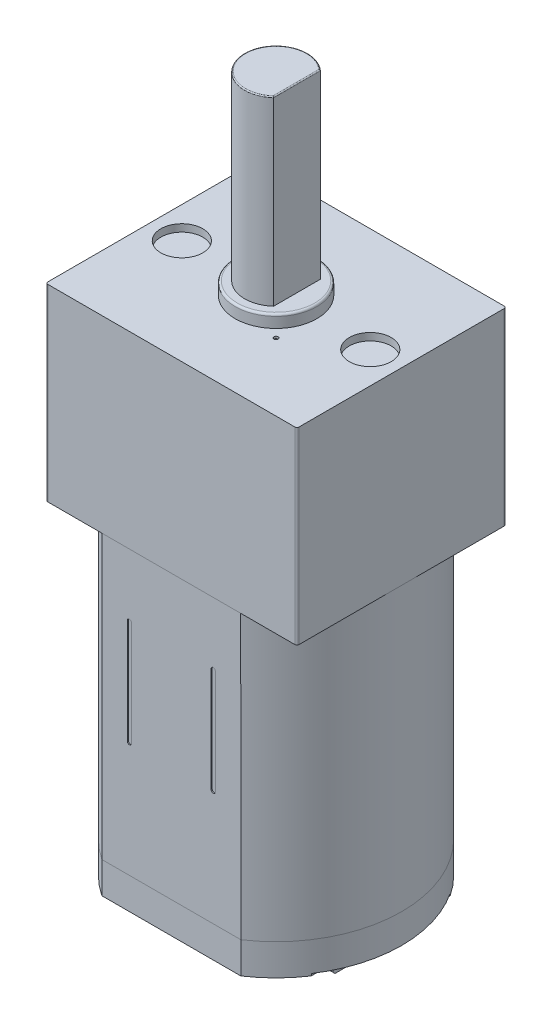
SolidWorks part; units mm, degrees
ref_plane "Спереди" through (0, 0, 0) normal (0, 0, 1) x (1, 0, 0)
ref_plane "Сверху" through (0, 0, 0) normal (0, 1, 0) x (1, 0, 0)
ref_plane "Справа" through (0, 0, 0) normal (1, 0, 0) x (0, 0, -1)
sketch "Эскиз1" plane through (0, 0, 0) normal (0, 1, 0) x (1, 0, 0)
  line L0 (-3.3166, 5) -> (3.3166, 5)
  line L1 (-3.3166, -5) -> (3.3166, -5)
  arc A0 (-3.3166, 5) -> (-3.3166, -5) centre (0, 0) ccw
  arc A1 (3.3166, -5) -> (3.3166, 5) centre (0, 0) ccw
  dimension "D1" = 12
  dimension "D2" = 5
  dimension "D3" = 5
extrude "Бобышка-Вытянуть1" add sketch "Эскиз1" along normal blind 13.5
sketch "Эскиз2" plane through (0, 13.5, 0) normal (0, 1, 0) x (1, 0, 0)
  line L1 (-6, 4.9983) -> (6, 4.9983)
  line L2 (-6, 4.9983) -> (-6, -5.0017)
  line L3 (-6, -5.0017) -> (6, -5.0017)
  line L4 (6, 4.9983) -> (6, -5.0017)
  dimension "D1" = 10
  dimension "D2" = 12
  dimension "D3" = 6
  dimension "D4" = 4.9983
extrude "Бобышка-Вытянуть2" add sketch "Эскиз2" along normal blind 9
sketch "Эскиз3" plane through (0, 22.5, 0) normal (0, 1, 0) x (1, 0, 0)
  circle A0 centre (0, 0) radius 1.95
  dimension "D1" = 3.9
extrude "Бобышка-Вытянуть3" add sketch "Эскиз3" along normal blind 0.6
sketch "Эскиз4" plane through (0, 23.1, 0) normal (0, 1, 0) x (1, 0, 0)
  line L0 (1, 1.118) -> (1, -1.118)
  arc A0 (1, 1.118) -> (1, -1.118) centre (0, 0) ccw
  point P5 (-1.5, 0)
  dimension "D1" = 3
  dimension "D2" = 2.5
extrude "Бобышка-Вытянуть4" add sketch "Эскиз4" along normal blind 8.67
sketch "Эскиз5" plane through (0, 22.5, 0) normal (0, 1, 0) x (1, 0, 0)
  line L0 (0, 4.9983) -> (0, -5.0017) construction
  line L1 (6, 4.9983) -> (-6, 4.9983) construction
  line L2 (-6, -5.0017) -> (6, -5.0017) construction
  circle A0 centre (-4.5, 0) radius 1
  circle A1 centre (4.5, 0) radius 1
  dimension "D3" = 2
  dimension "D1" = 4.5
  dimension "D2" = 4.9983
extrude "Вырез-Вытянуть1" cut sketch "Эскиз5" against normal blind 0.35
fillet "Скругление1" radius 0.1 4 edges
sketch "Эскиз6" plane through (0, 0, 0) normal (0, -1, 0) x (1, 0, 0)
  line L2 (-3.3166, -5) -> (3.3166, -5)
  line L3 (3.3166, 5) -> (-3.3166, 5)
  line L4 (-3.3166, -5) -> (3.3166, -5)
  line L5 (3.3166, 5) -> (-3.3166, 5)
  arc A2 (-3.3166, 5) -> (-3.3166, -5) centre (0, 0) ccw
  arc A3 (3.3166, -5) -> (3.3166, 5) centre (0, 0) ccw
  arc A4 (-3.3166, 5) -> (-3.3166, -5) centre (0, 0) ccw
  arc A5 (3.3166, -5) -> (3.3166, 5) centre (0, 0) ccw
  dimension "D1" = 0
extrude "Бобышка-Вытянуть6" add sketch "Эскиз6" along normal blind 1.4 separate body
sketch "Эскиз7" plane through (0, -1.4, 0) normal (0, -1, 0) x (-1, 0, 0)
  line L0 (5, -3.3166) -> (5, 3.3166)
  line L1 (-5, -3.3166) -> (-5, 3.3166)
  line L2 (3.3166, -5) -> (-3.3166, -5)
  line L3 (3.3166, 5) -> (-3.3176, 4.9987)
  arc A0 (3.3166, -5) -> (3.3166, 5) centre (0, 0) ccw construction
  arc A1 (-3.3166, 5) -> (-3.3166, -5) centre (0, 0) ccw construction
  arc A2 (3.3166, -5) -> (-3.3166, -5) centre (0, 0) ccw
  dimension "D1" = 5
  dimension "D2" = 5
extrude "Бобышка-Вытянуть7" add sketch "Эскиз7" along normal blind 0.1
sketch "Эскиз8" plane through (0, -1.5, 0) normal (0, -1, 0) x (-1, 0, 0)
  line L0 (5, 0) -> (-5, 0) construction
  line L1 (3.465, -0.75) -> (3.165, -0.75)
  line L2 (3.465, -0.75) -> (3.465, 0.75)
  line L3 (3.465, 0.75) -> (3.165, 0.75)
  line L4 (3.165, -0.75) -> (3.165, 0.75)
  line L5 (5, -3.3166) -> (5, 3.3166) construction
  line L6 (-5, -3.3166) -> (-5, 3.3166) construction
  line L7 (0, -5) -> (0, 5) construction
  line L8 (-3.3166, -5) -> (3.3166, -5) construction
  line L9 (3.3166, 5) -> (-3.3166, 5) construction
  line L10 (3.315, -0.75) -> (3.315, 0.75) construction
  line L11 (-3.315, -0.75) -> (-3.315, 0.75) construction
  line L12 (-3.165, -0.75) -> (-3.165, 0.75)
  line L13 (-3.465, 0.75) -> (-3.165, 0.75)
  line L14 (-3.465, -0.75) -> (-3.465, 0.75)
  line L15 (-3.465, -0.75) -> (-3.165, -0.75)
  dimension "D1" = 0.3
  dimension "D2" = 3.315
  dimension "D3" = 1.5
  dimension "D4" = 0.75
extrude "Бобышка-Вытянуть8" add sketch "Эскиз8" along normal blind 2
chamfer "Фаска1" distance 0.1 angle 45 4 edges at (3.315, -3.5, 0.75) (3.315, -3.5, -0.75) (-3.315, -3.5, 0.75) (-3.315, -3.5, -0.75)
sketch "Эскиз9" plane through (-3.465, 0, 0) normal (-1, 0, 0) x (0, 0, 1)
  line L0 (-0.75, -3.4) -> (-0.75, -1.5) construction
  line L1 (0.75, -1.5) -> (-0.75, -1.5) construction
  circle A0 centre (0, -2.5) radius 0.4
  dimension "D1" = 0.8
  dimension "D2" = 0.75
  dimension "D3" = 1
extrude "Вырез-Вытянуть2" cut sketch "Эскиз9" against normal blind 7
sketch "Эскиз10" plane through (0, -1.5, 0) normal (0, -1, 0) x (-1, 0, 0)
  circle A0 centre (0, 0) radius 2.5
  dimension "D1" = 5
extrude "Бобышка-Вытянуть9" add sketch "Эскиз10" along normal blind 2
fillet "Скругление2" radius 0.2 1 edges at (0, -3.5, -2.5)
sketch "Эскиз11" plane through (0, 23.1, 0) normal (0, 1, 0) x (1, 0, 0)
  line L0 (0, 0) -> (0, 4.9983)
  line L1 (5.9, 4.9983) -> (-5.9, 4.9983) construction
  line L2 (0, 0) -> (-6, -0.0017)
  line L3 (-6, 4.8983) -> (-6, -4.9017) construction
  line L4 (0, 0) -> (-1.7678, 1.7678)
  circle A0 centre (1.7678, -1.7678) radius 0.1
  circle A1 centre (-1.7678, 1.7678) radius 0.1
  point P14 (0, 0)
  dimension "D3" = 0.2
  dimension "D1" = 45
  dimension "D2" = 2.5
  dimension "D4" = 2
extrude "Вырез-Вытянуть3" cut sketch "Эскиз11" against normal blind 0.7
fillet "Скругление3" radius 0.1 1 edges at (0, -1.5, -2.5)
sketch "Эскиз12" plane through (0, 0, -5) normal (0, 0, -1) x (-1, 0, 0)
  line L0 (2, 5.5) -> (2, 10.5) construction
  line L1 (1.9, 5.5) -> (1.9, 10.5)
  line L2 (2.1, 5.5) -> (2.1, 10.5)
  line L3 (-2, 5.5) -> (-2, 10.5) construction
  line L4 (-2.1, 5.5) -> (-2.1, 10.5)
  line L5 (-1.9, 5.5) -> (-1.9, 10.5)
  line L6 (-3.3176, 13.5) -> (3.3176, 13.5) construction
  line L7 (0, -1.5) -> (0, 13.5) construction
  line L8 (3.3166, -1.5) -> (-3.3166, -1.5) construction
  arc A0 (1.9, 5.5) -> (2.1, 5.5) centre (2, 5.5) ccw
  arc A1 (2.1, 10.5) -> (1.9, 10.5) centre (2, 10.5) ccw
  arc A2 (-2.1, 5.5) -> (-1.9, 5.5) centre (-2, 5.5) ccw
  arc A3 (-1.9, 10.5) -> (-2.1, 10.5) centre (-2, 10.5) ccw
  point P2 (2, 8)
  point P7 (-2, 8)
  dimension "D1" = 0.1
  dimension "D2" = 0.1
  dimension "D3" = 5
  dimension "D4" = 5
  dimension "D5" = 3
  dimension "D6" = 3
  dimension "D7" = 2
  dimension "D8" = 2
extrude "Вырез-Вытянуть4" cut sketch "Эскиз12" against normal blind 0.05
ref_plane "Плоскость1" through (0, 0, 0) normal (0, 0, -1) x (-1, 0, 0)
mirror "Зеркальное отражение1" about plane through (0, 0, 0) normal (0, 0, -1) of "Вырез-Вытянуть4"
fillet "Скругление4" radius 0.05 2 edges at (1, 31.77, 0) (-1.5, 31.77, 0)
fillet "Скругление5" radius 0.1 1 edges at (0, 23.1, 1.95)
